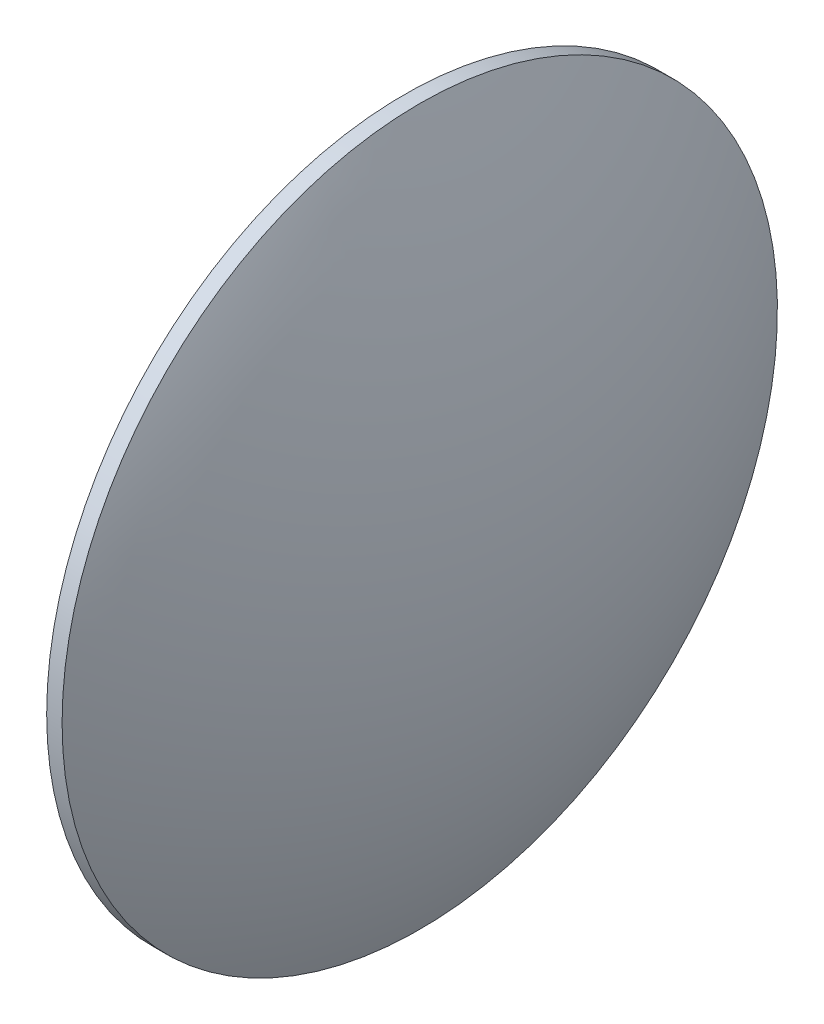
SolidWorks part; units mm, degrees
ref_plane "前视基准面" through (0, 0, 0) normal (0, 0, 1) x (1, 0, 0)
ref_plane "上视基准面" through (0, 0, 0) normal (0, 1, 0) x (1, 0, 0)
ref_plane "右视基准面" through (0, 0, 0) normal (1, 0, 0) x (0, 0, -1)
sketch "草图1" plane through (0, 0, 0) normal (0, 0, 1) x (1, 0, 0)
  line L0 (381.2896, 50.6632) -> (408.1811, 50.6632) construction
  line L1 (390.7244, 50.6632) -> (390.7244, 73.1632)
  line L2 (396.8244, 50.6632) -> (390.7244, 50.6632)
  line L5 (390.7244, 73.1632) -> (391.6944, 73.1632)
  arc A0 (396.8244, 50.6632) -> (391.6944, 73.1632) centre (344.9173, 50.6632) ccw
revolve "旋转1" add sketch "草图1" angle 360 about L0
